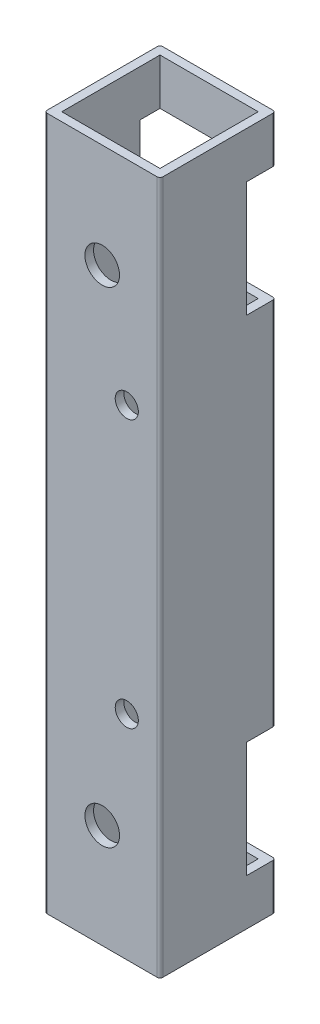
SolidWorks part; units mm, degrees
ref_plane "Front Plane" through (0, 0, 0) normal (0, 0, 1) x (1, 0, 0)
ref_plane "Top Plane" through (0, 0, 0) normal (0, 1, 0) x (1, 0, 0)
ref_plane "Right Plane" through (0, 0, 0) normal (1, 0, 0) x (0, 0, -1)
sketch "Sketch1" plane through (0, 0, 0) normal (0, 1, 0) x (1, 0, 0)
  line L0 (1.5, 1.5) -> (18.5, 1.5)
  line L1 (0.5, 0) -> (19.5, 0)
  line L2 (0, 0.5) -> (0, 19.5)
  line L3 (0.5, 20) -> (19.5, 20)
  line L4 (20, 0.5) -> (20, 19.5)
  line L5 (18.5, 1.5) -> (18.5, 18.5)
  line L6 (1.5, 18.5) -> (18.5, 18.5)
  line L7 (1.5, 1.5) -> (1.5, 18.5)
  arc A0 (19.5, 0) -> (20, 0.5) centre (19.5, 0.5) ccw
  arc A1 (0.5, 0) -> (0, 0.5) centre (0.5, 0.5) cw
  arc A2 (0, 19.5) -> (0.5, 20) centre (0.5, 19.5) cw
  arc A3 (19.5, 20) -> (20, 19.5) centre (19.5, 19.5) cw
  arc A4 (18.5, 1.5) -> (18.5, 1.5) centre (18.5, 1.5) ccw
  arc A5 (18.5, 18.5) -> (18.5, 18.5) centre (18.5, 18.5) cw
  arc A6 (1.5, 18.5) -> (1.5, 18.5) centre (1.5, 18.5) cw
  arc A7 (1.5, 1.5) -> (1.5, 1.5) centre (1.5, 1.5) cw
  point P9 (0, 0)
  dimension "D3" = 0.5
  dimension "D1" = 20
  dimension "D2" = 20
  dimension "D4" = 1.5
extrude "Boss-Extrude1" add sketch "Sketch1" along normal blind 120
sketch "Sketch2" plane through (20, 0, 0) normal (1, 0, 0) x (0, 0, -1)
  line L2 (15, 112) -> (15, 92)
  line L3 (15, 92) -> (20, 92)
  line L4 (20, 112) -> (20, 92)
  line L5 (20, 120) -> (20, 0) construction
  line L6 (20, 60) -> (0, 60) construction
  line L7 (0, 120) -> (0, 0) construction
  line L8 (20, 8) -> (20, 28)
  line L9 (15, 28) -> (20, 28)
  line L10 (15, 8) -> (15, 28)
  line L11 (15, 8) -> (20, 8)
  line L12 (20, 112) -> (15, 112)
  line L13 (0.5, 120) -> (19.5, 120) construction
  dimension "D1" = 8
  dimension "D2" = 5
  dimension "D3" = 20
extrude "Cut-Extrude1" cut sketch "Sketch2" against normal through all
sketch "Sketch3" plane through (0, 0, 0) normal (0, 0, 1) x (1, 0, 0)
  line L0 (19.5, 60) -> (0.5, 60) construction
  line L1 (19.5, 120) -> (19.5, 0) construction
  line L2 (0.5, 120) -> (0.5, 0) construction
  line L4 (0.5, 120) -> (19.5, 120) construction
  circle A0 centre (10, 102) radius 3
  circle A1 centre (10, 18) radius 3
  point P12 (10, 120)
  dimension "D1" = 18
  dimension "D2" = 6
extrude "Cut-Extrude2" cut sketch "Sketch3" against normal blind 100
sketch "Sketch4" plane through (0, 0, 0) normal (0, 0, 1) x (1, 0, 0)
  line L0 (20, 120) -> (20, 0) construction
  line L1 (19.5, 60) -> (3.2281, 60) construction
  line L2 (19.5, 120) -> (19.5, 0) construction
  circle A0 centre (14.25, 83.15) radius 2
  circle A1 centre (14.25, 36.85) radius 2
  dimension "D1" = 5.75
  dimension "D2" = 4
  dimension "D3" = 23.15
extrude "Cut-Extrude3" cut sketch "Sketch4" against normal blind 10
